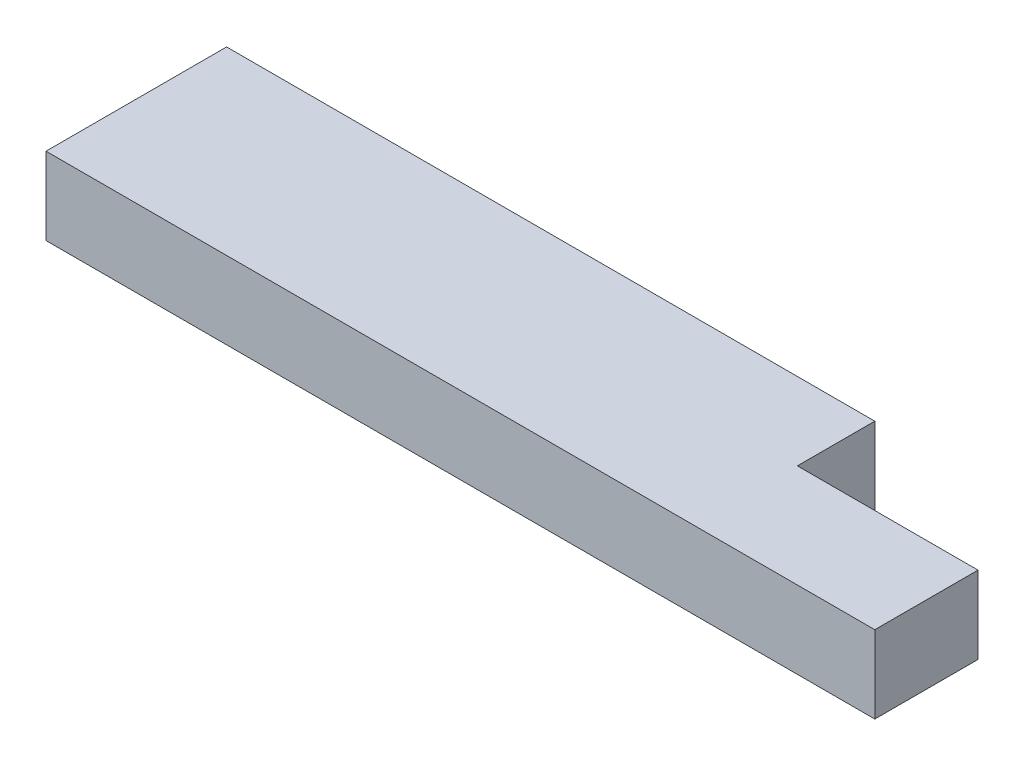
SolidWorks part; units mm, degrees
material "Pine"
ref_plane "Front Plane" through (0, 0, 0) normal (0, 0, 1) x (1, 0, 0)
ref_plane "Top Plane" through (0, 0, 0) normal (0, 1, 0) x (1, 0, 0)
ref_plane "Right Plane" through (0, 0, 0) normal (1, 0, 0) x (0, 0, -1)
sketch "Sketch1" plane through (0, 0, 0) normal (0, 1, 0) x (1, 0, 0)
  line L1 (0, 0) -> (319.0875, 0)
  line L2 (0, 0) -> (0, 88.9)
  line L3 (0, 88.9) -> (319.0875, 88.9)
  line L4 (319.0875, 0) -> (319.0875, 88.9)
  dimension "D1" = 88.9
  dimension "D2" = 319.0875
extrude "Boss-Extrude1" add sketch "Sketch1" along normal blind 38.1
sketch "Sketch2" plane through (0, 0, 0) normal (0, -1, 0) x (1, 0, 0)
  line L1 (319.0875, -50.8) -> (407.9875, -50.8)
  line L2 (319.0875, -50.8) -> (319.0875, 0)
  line L3 (319.0875, 0) -> (407.9875, 0)
  line L4 (407.9875, -50.8) -> (407.9875, 0)
  line L7 (319.0875, 0) -> (319.0875, -88.9) construction
  line L8 (0, 0) -> (319.0875, 0) construction
  dimension "D1" = 407.9875
  dimension "D2" = 50.8
extrude "Boss-Extrude2" add sketch "Sketch2" against normal through all
